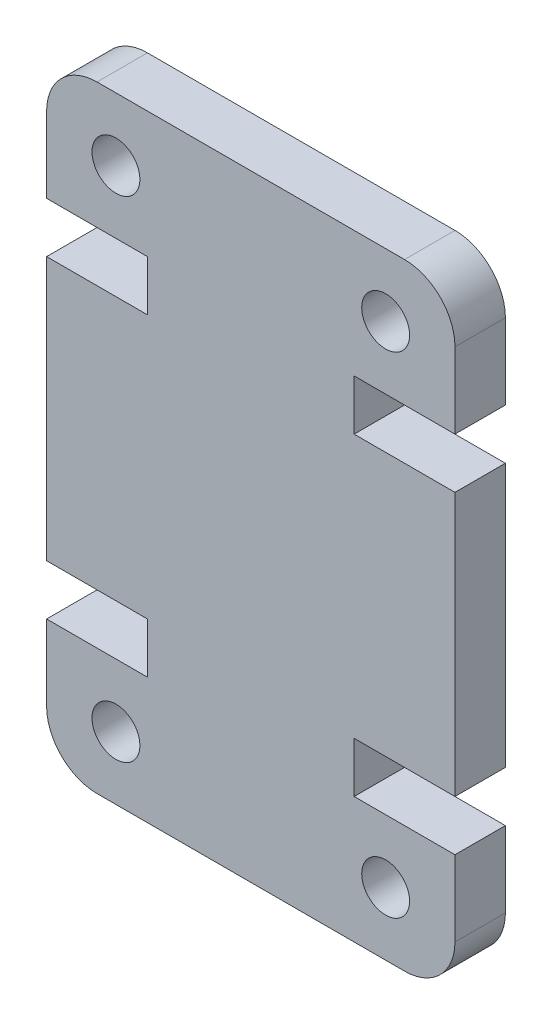
SolidWorks part; units mm, degrees
ref_plane "Front Plane" through (0, 0, 0) normal (0, 0, 1) x (1, 0, 0)
ref_plane "Top Plane" through (0, 0, 0) normal (0, 1, 0) x (1, 0, 0)
ref_plane "Right Plane" through (0, 0, 0) normal (1, 0, 0) x (0, 0, -1)
sketch "Sketch1" plane through (0, 0, 0) normal (0, 0, 1) x (1, 0, 0)
  line L0 (0, 17.45) -> (0, 7)
  line L1 (16.2, 5) -> (16.2, 2)
  line L2 (12.2, 5) -> (16.2, 5)
  line L3 (2, 0) -> (14.2, 0)
  line L4 (16.2, 7) -> (12.2, 7)
  line L5 (12.2, 7) -> (12.2, 5)
  line L6 (16.2, 17.45) -> (16.2, 7)
  line L7 (0, 19.45) -> (0, 22.45)
  line L8 (4, 19.45) -> (0, 19.45)
  line L9 (0, 17.45) -> (4, 17.45)
  line L10 (4, 7) -> (4, 5)
  line L11 (4, 17.45) -> (4, 19.45)
  line L12 (0, 7) -> (4, 7)
  line L13 (4, 5) -> (0, 5)
  line L14 (12.2, 17.45) -> (12.2, 19.45)
  line L15 (16.2, 17.45) -> (12.2, 17.45)
  line L16 (2, 24.45) -> (14.2, 24.45)
  line L17 (12.2, 19.45) -> (16.2, 19.45)
  line L18 (16.2, 19.45) -> (16.2, 22.45)
  line L19 (0, 5) -> (0, 2)
  line L20 (0, 12.225) -> (16.2, 12.225) construction
  line L21 (8.1, 24.45) -> (8.1, 0) construction
  circle A0 centre (13.45, 2.5) radius 0.95
  arc A1 (16.2, 2) -> (14.2, 0) centre (14.2, 2) cw
  circle A2 centre (2.75, 21.95) radius 0.95
  arc A3 (0, 2) -> (2, 0) centre (2, 2) ccw
  arc A4 (0, 22.45) -> (2, 24.45) centre (2, 22.45) cw
  circle A5 centre (2.75, 2.5) radius 0.95
  arc A6 (16.2, 22.45) -> (14.2, 24.45) centre (14.2, 22.45) ccw
  circle A7 centre (13.45, 21.95) radius 0.95
  point P17 (8.1, 12.225)
  dimension "D1" = 1.9
  dimension "D2" = 2
  dimension "D3" = 2.75
  dimension "D4" = 8.1
  dimension "D5" = 2.5
  dimension "D6" = 5
  dimension "D8" = 12.225
extrude "Boss-Extrude1" add sketch "Sketch1" along normal blind 4
sketch "Sketch2" plane through (0, 0, 0) normal (0, 0, -1) x (-1, 0, 0)
  line L0 (0, 0) -> (0, 24.45)
  line L1 (0, 24.45) -> (-16.2, 24.45)
  line L2 (-16.2, 24.45) -> (-16.2, 0)
  line L3 (-16.2, 0) -> (0, 0)
extrude "Cut-Extrude1" cut sketch "Sketch2" against normal blind 2
equation "\"D4@Sketch1\"= \"fingerWidth@parametersSketch@prostheticParameters.SLDPRT\" / 2 'MIP Width"
equation "\"D8@Sketch1\"= ( ( \"HL@parametersSketch@prostheticParameters.SLDPRT\" * 0.17 ) - 4 - 3 ) / 2 'MIP Length - Sil. Sht MIP - Sil. Sht DIP"
equation "\"D1@Sketch1\"= 1.5 + \"tol1@parametersSketch@prostheticParameters.SLDPRT\""
